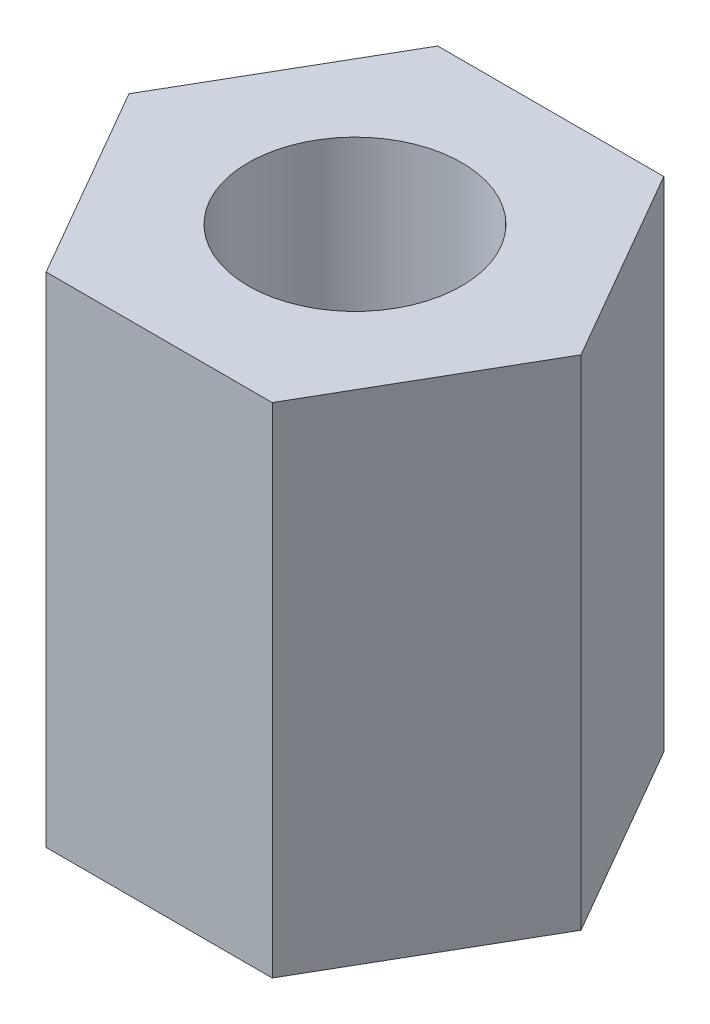
SolidWorks part; units mm, degrees
ref_plane "前视基准面" through (0, 0, 0) normal (0, 0, 1) x (1, 0, 0)
ref_plane "上视基准面" through (0, 0, 0) normal (0, 1, 0) x (1, 0, 0)
ref_plane "右视基准面" through (0, 0, 0) normal (1, 0, 0) x (0, 0, -1)
other "Configuration Table"
sketch "草图1" plane through (0, 0, 0) normal (0, 1, 0) x (1, 0, 0)
  line L1 (3.1754, 0) -> (1.5877, 2.75)
  line L2 (1.5877, 2.75) -> (-1.5877, 2.75)
  line L3 (-1.5877, 2.75) -> (-3.1754, 0)
  line L4 (-3.1754, 0) -> (-1.5877, -2.75)
  line L5 (-1.5877, -2.75) -> (1.5877, -2.75)
  line L6 (1.5877, -2.75) -> (3.1754, 0)
  circle A0 centre (0, 0) radius 2.75 construction
  circle A1 centre (0, 0) radius 1.5
extrude "凸台-拉伸1" add sketch "草图1" along normal blind 7
